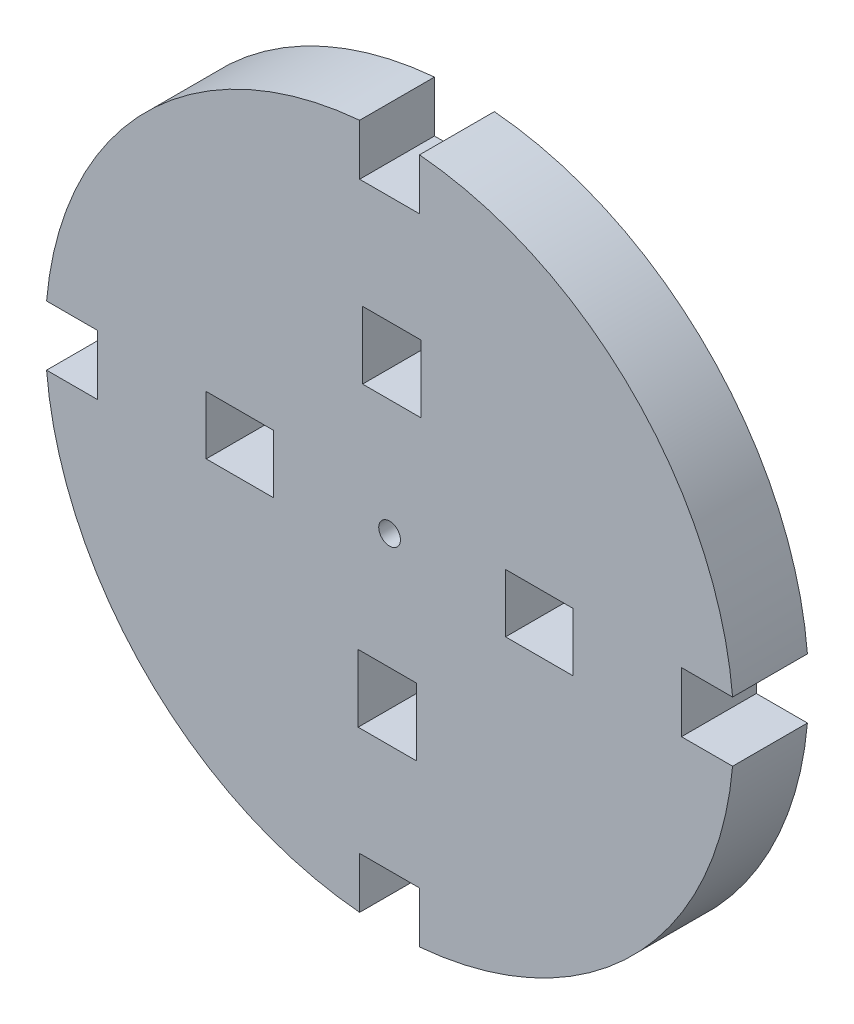
SolidWorks part; units mm, degrees
ref_plane "Front Plane" through (0, 0, 0) normal (0, 0, 1) x (1, 0, 0)
ref_plane "Top Plane" through (0, 0, 0) normal (0, 1, 0) x (1, 0, 0)
ref_plane "Right Plane" through (0, 0, 0) normal (1, 0, 0) x (0, 0, -1)
sketch "Sketch1" plane through (0, 0, 0) normal (0, 0, 1) x (1, 0, 0)
  circle A0 centre (0, 0) radius 23
  circle A1 centre (0, 0) radius 0.725
  dimension "D1" = 46
  dimension "D2" = 1.45
extrude "Boss-Extrude1" add sketch "Sketch1" along normal blind 5
sketch "Sketch2" plane through (0, 0, 0) normal (0, 0, -1) x (-1, 0, 0)
  line L0 (12.2499, -1.8012) -> (7.7499, -1.8012)
  line L1 (-2.0978, 12.2489) -> (1.8022, 12.2489)
  line L2 (-2.0978, 12.2489) -> (-2.0978, 7.7489)
  line L3 (-2.0978, 7.7489) -> (1.8022, 7.7489)
  line L4 (1.8022, 12.2489) -> (1.8022, 7.7489)
  line L5 (-2.0978, 12.2489) -> (1.8022, 7.7489) construction
  line L6 (-2.0978, 7.7489) -> (1.8022, 12.2489) construction
  line L7 (12.2499, 2.0988) -> (12.2499, -1.8012)
  line L8 (12.2499, 2.0988) -> (7.7499, 2.0988)
  line L9 (7.7499, 2.0988) -> (7.7499, -1.8012)
  line L10 (-1.8002, -12.2489) -> (-1.8002, -7.7489)
  line L11 (2.0998, -12.2489) -> (-1.8002, -12.2489)
  line L12 (2.0998, -12.2489) -> (2.0998, -7.7489)
  line L13 (2.0998, -7.7489) -> (-1.8002, -7.7489)
  line L14 (-12.2479, 1.8012) -> (-7.7479, 1.8012)
  line L15 (-12.2479, -2.0988) -> (-12.2479, 1.8012)
  line L16 (-12.2479, -2.0988) -> (-7.7479, -2.0988)
  line L17 (-7.7479, -2.0988) -> (-7.7479, 1.8012)
  point P0 (-0.1478, 9.9989)
  point P5 (0, 0)
  dimension "D1" = 3.9
  dimension "D2" = 4.5
  dimension "D3" = 10
  dimension "D4" = 4
extrude "Cut-Extrude1" cut sketch "Sketch2" against normal through all
sketch "Sketch3" plane through (0, 0, 0) normal (0, 0, -1) x (-1, 0, 0)
  line L0 (26.5, 2) -> (19.5, 2)
  line L1 (-2, 26.5) -> (2, 26.5)
  line L2 (-2, 26.5) -> (-2, 19.5)
  line L3 (-2, 19.5) -> (2, 19.5)
  line L4 (2, 26.5) -> (2, 19.5)
  line L5 (-2, 26.5) -> (2, 19.5) construction
  line L6 (-2, 19.5) -> (2, 26.5) construction
  line L7 (26.5, 2) -> (26.5, -2)
  line L8 (26.5, -2) -> (19.5, -2)
  line L9 (19.5, 2) -> (19.5, -2)
  line L10 (2, -26.5) -> (2, -19.5)
  line L11 (2, -26.5) -> (-2, -26.5)
  line L12 (-2, -26.5) -> (-2, -19.5)
  line L13 (2, -19.5) -> (-2, -19.5)
  line L14 (-26.5, -2) -> (-19.5, -2)
  line L15 (-26.5, -2) -> (-26.5, 2)
  line L16 (-26.5, 2) -> (-19.5, 2)
  line L17 (-19.5, -2) -> (-19.5, 2)
  circle A0 centre (0, 0) radius 23 construction
  point P0 (0, 23)
  point P7 (0, 0)
  dimension "D1" = 4
  dimension "D2" = 7
  dimension "D3" = 4
extrude "Cut-Extrude2" cut sketch "Sketch3" against normal through all
sketch "Sketch4" plane through (0, 0, 0) normal (0, 0, -1) x (-1, 0, 0)
  circle A0 centre (0, 0) radius 20
  dimension "D1" = 40
